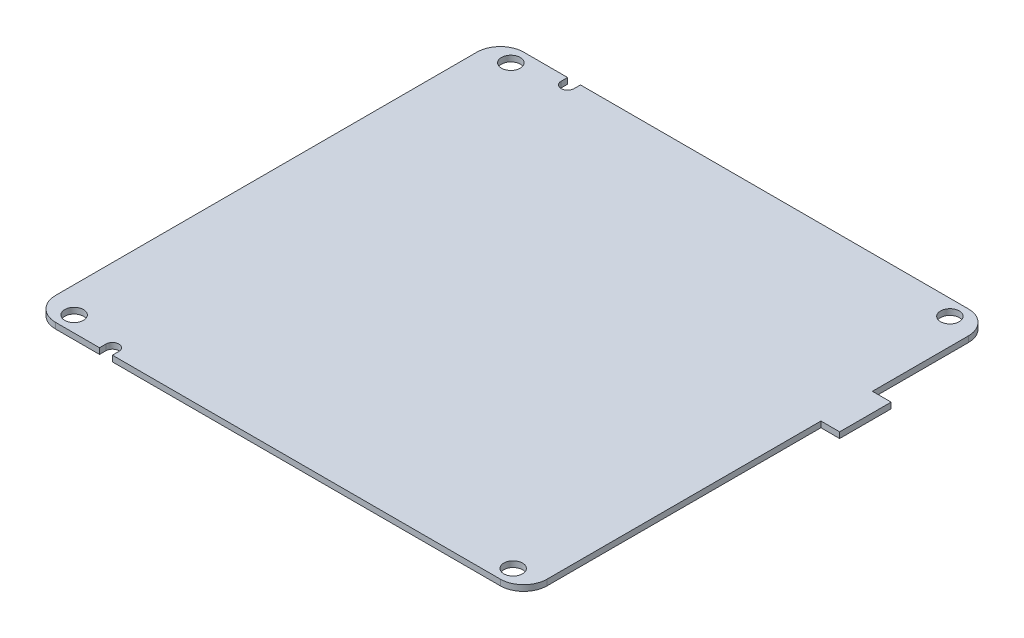
SolidWorks part; units mm, degrees
ref_plane "Front Plane" through (0, 0, 0) normal (0, 0, 1) x (1, 0, 0)
ref_plane "Top Plane" through (0, 0, 0) normal (0, 1, 0) x (1, 0, 0)
ref_plane "Right Plane" through (0, 0, 0) normal (1, 0, 0) x (0, 0, -1)
sketch "Sketch1" plane through (0, 0, 0) normal (0, 1, 0) x (1, 0, 0)
  line L1 (-52.5, 50) -> (52.5, 50)
  line L2 (-52.5, 50) -> (-52.5, -50)
  line L3 (-52.5, -50) -> (52.5, -50)
  line L4 (52.5, 50) -> (52.5, -50)
  line L5 (-52.5, 50) -> (52.5, -50) construction
  line L6 (-52.5, -50) -> (52.5, 50) construction
  line L7 (52.5, 24.5) -> (56.5, 24.5)
  line L8 (52.5, 24.5) -> (52.5, 13.5)
  line L9 (52.5, 13.5) -> (56.5, 13.5)
  line L10 (56.5, 24.5) -> (56.5, 13.5)
  point P0 (0, 0)
  dimension "D1" = 105
  dimension "D2" = 100
  dimension "D3" = 36.5
  dimension "D4" = 11
  dimension "D5" = 4
extrude "Main PCB" add sketch "Sketch1" along normal blind 1.25 contours L4 L1 L2 L3 | L10 L7 L4 L9
fillet "Main PCB rounded corners" radius 5 4 edges at (52.5, 0.625, 50) (-52.5, 0.625, 50) (-52.5, 0.625, -50) (52.5, 0.625, -50)
sketch "Sketch2" plane through (0, 1.25, 0) normal (0, 1, 0) x (1, 0, 0)
  line L0 (-52.5, 0) -> (52.5, 0) construction
  line L3 (0, 50) -> (0, -50) construction
  line L6 (-38.125, -48.625) -> (-38.125, -50)
  line L7 (-35.375, -48.625) -> (-35.375, -50)
  line L8 (-35.375, 48.625) -> (-35.375, 50)
  line L9 (-38.125, 48.625) -> (-38.125, 50)
  line L10 (-47.5, -50) -> (47.5, -50) construction
  line L11 (-52.5, 45) -> (-52.5, -45) construction
  line L12 (-47.5, 50) -> (47.5, 50) construction
  line L15 (52.5, 13.5) -> (52.5, -45) construction
  circle A0 centre (-46.9, -46.65) radius 2
  circle A1 centre (46.9, -46.65) radius 2
  circle A2 centre (46.9, 46.65) radius 2
  circle A3 centre (-46.9, 46.65) radius 2
  circle A4 centre (-36.75, -48.625) radius 1.375
  circle A5 centre (-36.75, 48.625) radius 1.375
  point P2 (0, 0)
  point P5 (0, 0)
  point P10 (0, 0)
  point P11 (0, 0)
  point P32 (0, 0)
  point P33 (0, 0)
  point P34 (0, 0)
  point P37 (0, 0)
  point P40 (0, 0)
  point P41 (0, 0)
  dimension "D1" = 93.8
  dimension "D3" = 4
  dimension "D4" = 2.75
  dimension "D2" = 93.3
  dimension "D5" = 15.75
extrude "Main PCB holes" cut sketch "Sketch2" against normal up to next
